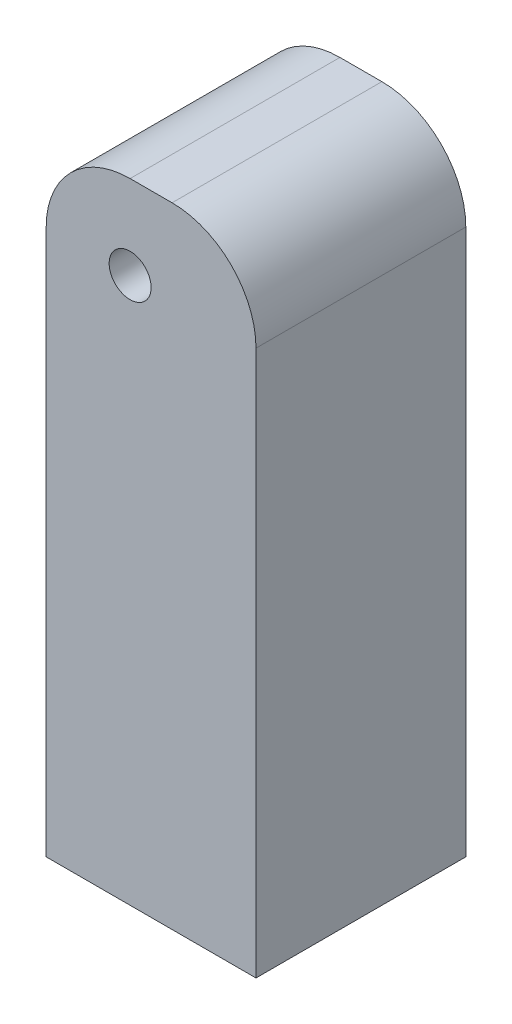
SolidWorks part; units mm, degrees
ref_plane "Front Plane" through (0, 0, 0) normal (0, 0, 1) x (1, 0, 0)
ref_plane "Top Plane" through (0, 0, 0) normal (0, 1, 0) x (1, 0, 0)
ref_plane "Right Plane" through (0, 0, 0) normal (1, 0, 0) x (0, 0, -1)
sketch "Sketch1" plane through (0, 0, 0) normal (0, 0, 1) x (1, 0, 0)
  line L1 (150, 25) -> (160, 25)
  line L2 (130, 5) -> (130, -125)
  line L3 (130, -125) -> (180, -125)
  line L4 (180, 5) -> (180, -125)
  arc A0 (160, 25) -> (180, 5) centre (160, 5) cw
  arc A1 (150, 25) -> (130, 5) centre (150, 5) ccw
  circle A2 centre (150, 5) radius 5
  point P7 (180, 25)
  point P10 (130, 25)
  dimension "D3" = 20
  dimension "D4" = 10
  dimension "D1" = 150
  dimension "D2" = 50
extrude "Boss-Extrude1" add sketch "Sketch1" along normal mid plane 50
sketch "Sketch2" plane through (0, -125, 0) normal (0, -1, 0) x (1, 0, 0)
  line L0 (180, 25) -> (180, -25) construction
  line L1 (130, 25) -> (180, 25) construction
  circle A0 centre (155, 0) radius 10
  dimension "D1" = 20
  dimension "D2" = 25
  dimension "D3" = 25
extrude "Cut-Extrude1" cut sketch "Sketch2" against normal blind 50
scale "Scale1" bodies to scale 102 scale about centroid uniform scaling yes scale factor 0.3
